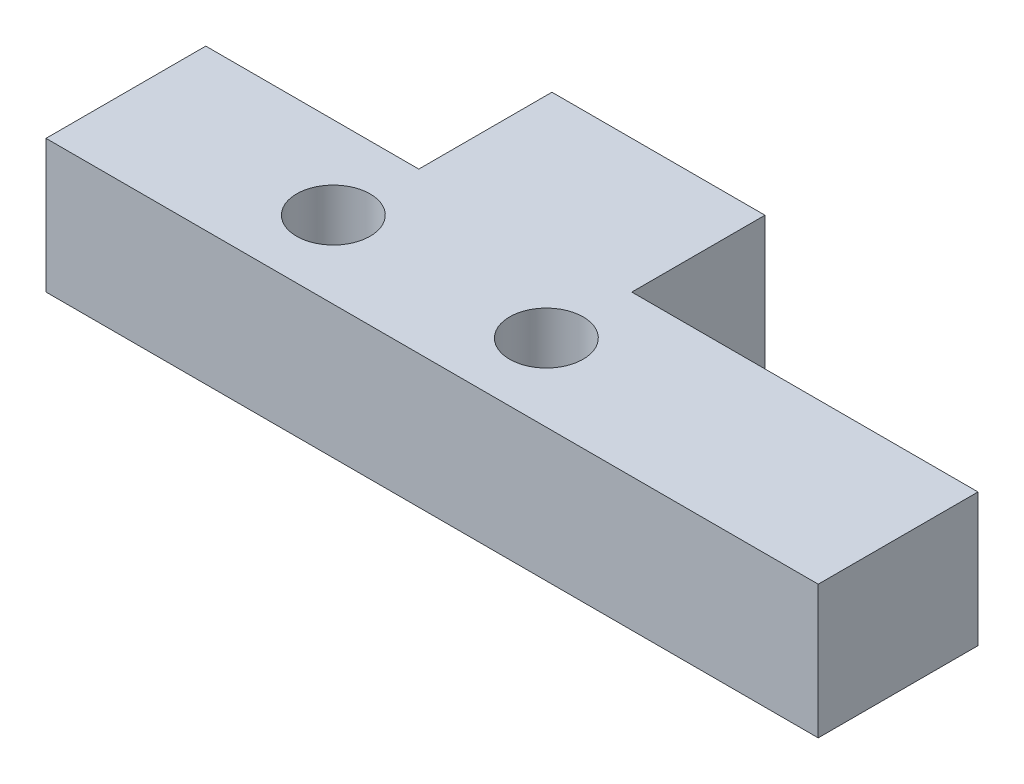
SolidWorks part; units mm, degrees
ref_plane "Front Plane" through (0, 0, 0) normal (0, 0, 1) x (1, 0, 0)
ref_plane "Top Plane" through (0, 0, 0) normal (0, 1, 0) x (1, 0, 0)
ref_plane "Right Plane" through (0, 0, 0) normal (1, 0, 0) x (0, 0, -1)
sketch "Sketch1" plane through (0, 0, 0) normal (0, 1, 0) x (1, 0, 0)
  line L1 (-15.24, -3.81) -> (15.24, -3.81)
  line L2 (-15.24, -3.81) -> (-15.24, 3.81)
  line L3 (-15.24, 3.81) -> (15.24, 3.81)
  line L4 (15.24, -3.81) -> (15.24, 3.81)
  line L5 (-15.24, -3.81) -> (15.24, 3.81) construction
  line L6 (-15.24, 3.81) -> (15.24, -3.81) construction
  point P0 (0, 0)
  dimension "D1" = 7.62
  dimension "D2" = 30.48
extrude "Boss-Extrude1" add sketch "Sketch1" along normal mid plane 6.35
sketch "Sketch2" plane through (0, 3.175, 0) normal (0, 1, 0) x (1, 0, 0)
  line L0 (15.24, 3.81) -> (-15.24, 3.81) construction
  line L1 (-5.08, 3.81) -> (5.08, 3.81)
  line L2 (-5.08, 3.81) -> (-5.08, 10.16)
  line L3 (-5.08, 10.16) -> (5.08, 10.16)
  line L4 (5.08, 3.81) -> (5.08, 10.16)
  line L5 (-15.24, 3.81) -> (-5.08, 3.81) construction
  line L6 (5.08, 3.81) -> (15.24, 3.81) construction
extrude "Boss-Extrude2" add sketch "Sketch2" against normal blind 6.35
sketch "Sketch3" plane through (0, 3.175, 0) normal (0, 1, 0) x (1, 0, 0)
  line L1 (15.24, 3.81) -> (21.59, 3.81)
  line L2 (15.24, 3.81) -> (15.24, -3.81)
  line L3 (15.24, -3.81) -> (21.59, -3.81)
  line L4 (21.59, 3.81) -> (21.59, -3.81)
extrude "Boss-Extrude3" add sketch "Sketch3" against normal blind 6.35
sketch "Sketch6" plane through (0, -3.175, 0) normal (0, -1, 0) x (1, 0, 0)
  circle A0 centre (4.9416, 0.127) radius 1.7526 construction
  circle A1 centre (-5.2184, 0.127) radius 1.7526 construction
  circle A2 centre (4.9416, 0.127) radius 1.7526
  circle A3 centre (-5.2184, 0.127) radius 1.7526
extrude "Cut-Extrude1" cut sketch "Sketch6" against normal through all
equation "\"material\"=\"GMaterial@Platform.assembly\""
equation "\"D1@Boss-Extrude1\"=\"material\""
equation "\"D1@Boss-Extrude2\"=\"material\""
equation "\"D1@Boss-Extrude3\"=\"material\""
